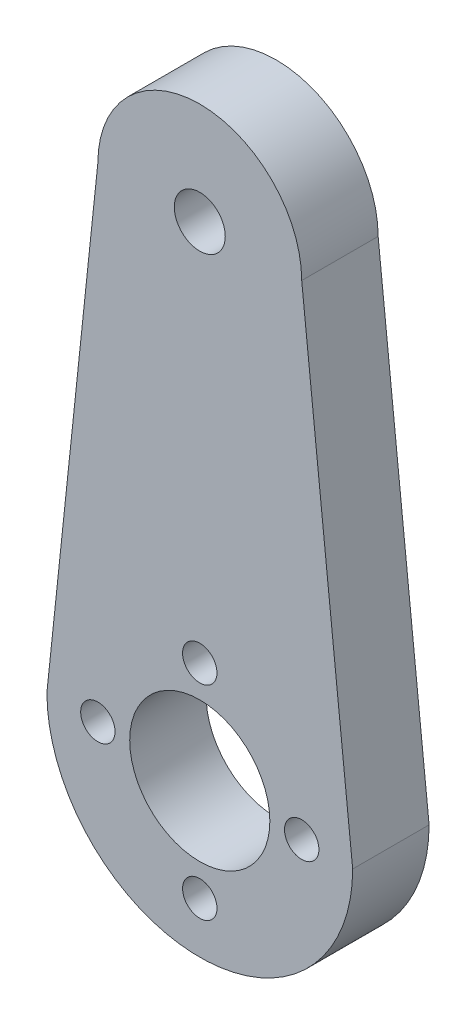
SolidWorks part; units mm, degrees
ref_plane "Front" through (0, 0, 0) normal (0, 0, 1) x (1, 0, 0)
ref_plane "Top" through (0, 0, 0) normal (0, 1, 0) x (1, 0, 0)
ref_plane "Right" through (0, 0, 0) normal (1, 0, 0) x (0, 0, -1)
sketch "Esquisse1" plane through (0, 0, 0) normal (0, 0, 1) x (1, 0, 0)
  line L0 (0, 0) -> (0, 38) construction
  line L1 (12, 0) -> (8, 38)
  line L2 (0, 58) -> (0, 38) construction
  line L3 (0, -12) -> (0, 0) construction
  line L4 (12, 0) -> (-12, 0) construction
  line L5 (8, 38) -> (-8, 38) construction
  line L6 (-12, 0) -> (-8, 38)
  arc A0 (8, 38) -> (-8, 38) centre (0, 38) ccw
  arc A1 (12, 0) -> (-12, 0) centre (0, 0) cw
  dimension "D2" = 12
  dimension "D3" = 8
  dimension "D1" = 38
extrude "Boss.-Extru.1" add sketch "Esquisse1" along normal blind 6
sketch "Esquisse2" plane through (0, 0, 6) normal (0, 0, 1) x (1, 0, 0)
  line L0 (0, 0) -> (8, 0) construction
  circle A0 centre (0, 0) radius 5.5
  circle A1 centre (8, 0) radius 1.35
  circle A2 centre (0, -8) radius 1.35
  circle A3 centre (-8, 0) radius 1.35
  circle A4 centre (0, 8) radius 1.35
  circle A5 centre (0, 38) radius 2
  point P14 (0, 0)
  dimension "D1" = 11
  dimension "D2" = 2.7
  dimension "D5" = 4
  dimension "D3" = 8
  dimension "D4" = 4
extrude "Enlèv. mat.-Extru.1" cut sketch "Esquisse2" against normal through all both and the other way through all
